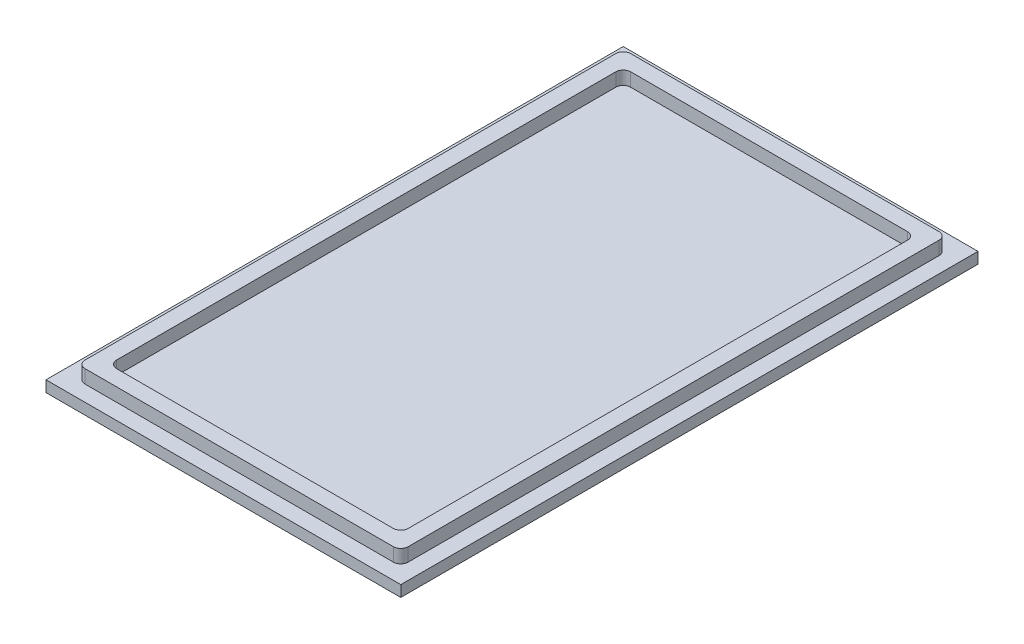
SolidWorks part; units mm, degrees
ref_plane "Front Plane" through (0, 0, 0) normal (0, 0, 1) x (1, 0, 0)
ref_plane "Top Plane" through (0, 0, 0) normal (0, 1, 0) x (1, 0, 0)
ref_plane "Right Plane" through (0, 0, 0) normal (1, 0, 0) x (0, 0, -1)
sketch "PCB Dimensions" plane through (0, 0, 0) normal (0, 1, 0) x (1, 0, 0)
  line L0 (0, 0) -> (-3.5355, 3.5355)
  line L1 (0, 0) -> (40.6457, 0)
  line L2 (0, 0) -> (0, -70.5657)
  line L3 (0, -70.5657) -> (40.6457, -70.5657)
  line L4 (40.6457, 0) -> (40.6457, -70.5657)
  line L5 (40.6457, -70.5657) -> (44.1812, -74.1012)
  line L6 (40.6457, 0) -> (44.1812, 3.5355)
  line L11 (0, -70.5657) -> (-3.5355, -74.1012)
  line L12 (44.1812, -74.1012) -> (-3.5355, -74.1012)
  line L13 (44.1812, -74.1012) -> (44.1812, 3.5355)
  line L14 (44.1812, 3.5355) -> (-3.5355, 3.5355)
  line L15 (-3.5355, -74.1012) -> (-3.5355, 3.5355)
extrude "Boss-Extrude3" add sketch "PCB Dimensions" along normal blind 1.5 contours L14 L15 L12 L13
sketch "Sketch5" plane through (0, 1.5, 0) normal (0, 1, 0) x (1, 0, 0)
  line L11 (-1.4142, 1.4142) -> (42.0599, 1.4142)
  line L12 (-1.4142, 1.4142) -> (-1.4142, -71.9799)
  line L13 (-1.4142, -71.9799) -> (42.0599, -71.9799)
  line L14 (42.0599, 1.4142) -> (42.0599, -71.9799)
  line L17 (0.7071, -0.7071) -> (39.9386, -0.7071)
  line L18 (0.7071, -0.7071) -> (0.7071, -69.8586)
  line L19 (0.7071, -69.8586) -> (39.9386, -69.8586)
  line L20 (39.9386, -0.7071) -> (39.9386, -69.8586)
extrude "Boss-Extrude4" add sketch "Sketch5" along normal blind 1.8 contours L13 L14 L11 L12 | L18 L19 L20 L17
fillet "Fillet1" radius 1 8 edges at (0.7071, 2.4, 69.8586) (-1.4142, 2.4, 71.9799) (39.9386, 2.4, 69.8586) (42.0599, 2.4, 71.9799) (0.7071, 2.4, 0.7071) (39.9386, 2.4, 0.7071) (42.0599, 2.4, -1.4142) (-1.4142, 2.4, -1.4142)
sketch "Sketch6" plane through (0, 0, 0) normal (0, -1, 0) x (1, 0, 0)
  line L0 (8.3228, 67.2497) -> (32.3228, 67.2497)
  line L1 (8.3228, 67.2497) -> (8.3228, 3.2497)
  line L2 (8.3228, 3.2497) -> (32.3228, 3.2497)
  line L3 (32.3228, 67.2497) -> (32.3228, 3.2497)
  line L4 (20.3228, 74.1012) -> (20.3228, -3.5355)
  line L5 (44.1812, 74.1012) -> (-3.5355, 74.1012) construction
  line L6 (44.1812, -3.5355) -> (-3.5355, -3.5355) construction
  line L7 (-3.5355, 35.2828) -> (44.1812, 35.2828)
  line L8 (-3.5355, 74.1012) -> (-3.5355, -3.5355) construction
  line L9 (44.1812, 74.1012) -> (44.1812, -3.5355) construction
extrude "Boss-Extrude5" add sketch "Sketch6" along normal blind 10 contours L1 L7 L4 L0 | L4 L7 L3 L0 | L7 L1 L2 L4 | L7 L4 L2 L3
sketch "Sketch7" plane through (32.3228, 0, 0) normal (1, 0, 0) x (0, 0, -1)
  line L0 (-59.2497, 0) -> (-11.2497, 0)
  line L1 (-59.2497, 0) -> (-59.2497, -6)
  line L2 (-59.2497, -6) -> (-11.2497, -6)
  line L3 (-11.2497, 0) -> (-11.2497, -6)
extrude "Cut-Extrude1" cut sketch "Sketch7" against normal blind 24
fillet "Fillet2" radius 6 2 edges at (20.3228, -10, 3.2497) (20.3228, -10, 67.2497)
fillet "Fillet3" radius 1 2 edges at (20.3228, -6, 11.2497) (20.3228, -6, 59.2497)
scale "Scale1" bodies to scale 112 scale about centroid uniform scaling yes scale factor 0.99
